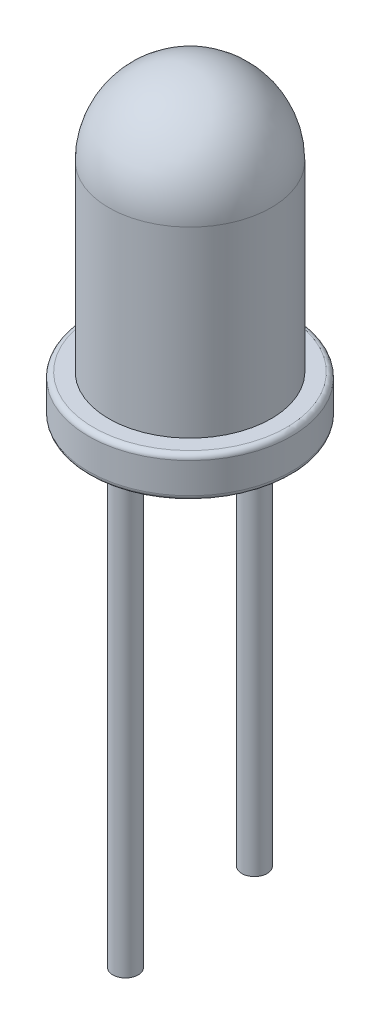
SolidWorks part; units mm, degrees
ref_plane "Front Plane" through (0, 0, 0) normal (0, 0, 1) x (1, 0, 0)
ref_plane "Top Plane" through (0, 0, 0) normal (0, 1, 0) x (1, 0, 0)
ref_plane "Right Plane" through (0, 0, 0) normal (1, 0, 0) x (0, 0, -1)
sketch "Sketch1" plane through (0, 0, 0) normal (0, 0, 1) x (1, 0, 0)
  line L0 (2, 0) -> (-2, 0)
  line L1 (-2, 0) -> (-2, 0.8)
  line L2 (-2, 0.8) -> (-1.6, 0.8)
  line L3 (2, 0.8) -> (2, 0)
  line L4 (0, 8.5983) -> (0, -1.7115) construction
  line L5 (-1.6, 0.8) -> (-1.6, 4.4)
  line L7 (1.6, 4.4) -> (1.6, 0.8)
  line L8 (1.6, 0.8) -> (2, 0.8)
  arc A0 (-1.6, 4.4) -> (1.6, 4.4) centre (0, 4.4) cw
  dimension "D1" = 0.8
  dimension "D2" = 4
  dimension "D3" = 0.4
  dimension "D4" = 0.4
revolve "Revolve6" add sketch "Sketch1" angle 360 about L4
fillet "Fillet1" radius 0.1 2 edges at (0, 0, 2) (0, 0.8, 2)
sketch "Sketch2" plane through (0, 0, 0) normal (0, -1, 0) x (1, 0, 0)
  line L0 (2.1557, 0) -> (-2.8577, 0) construction
  circle A0 centre (-1.27, 0) radius 0.25
  dimension "D1" = 0.5
  dimension "D2" = 1.27
extrude "Boss-Extrude1" add sketch "Sketch2" along normal blind 10
sketch "Sketch3" plane through (0, 0, 0) normal (0, -1, 0) x (1, 0, 0)
  line L0 (2.6145, 0) -> (-2.6587, 0) construction
  circle A0 centre (1.27, 0) radius 0.25
  dimension "D1" = 0.5
  dimension "D2" = 1.27
extrude "Boss-Extrude2" add sketch "Sketch3" along normal blind 7
